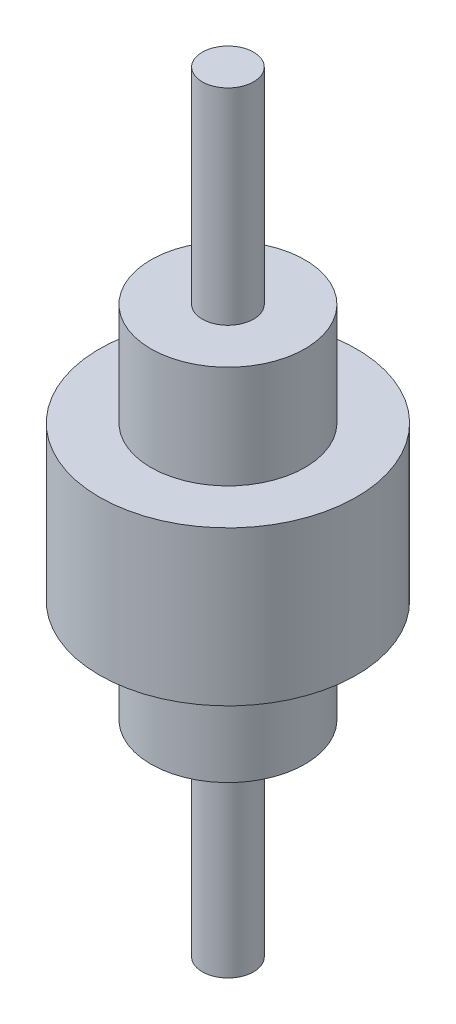
SolidWorks part; units mm, degrees
ref_plane "Front Plane" through (0, 0, 0) normal (0, 0, 1) x (1, 0, 0)
ref_plane "Top Plane" through (0, 0, 0) normal (0, 1, 0) x (1, 0, 0)
ref_plane "Right Plane" through (0, 0, 0) normal (1, 0, 0) x (0, 0, -1)
sketch "Sketch1" plane through (0, 0, 0) normal (0, 0, 1) x (1, 0, 0)
  line L0 (0, 0) -> (0, -203.8323) construction
  line L1 (0, -203.8323) -> (0, 170.1772) construction
  line L2 (10, 48.2971) -> (30, 48.2971)
  line L3 (50, -51.7029) -> (30, -51.7029)
  line L4 (30, 48.2971) -> (30, 8.2971)
  line L5 (30, 8.2971) -> (50, 8.2971)
  line L6 (50, -51.7029) -> (50, 8.2971)
  line L7 (10, 128.2971) -> (0, 128.2971)
  line L8 (10, 48.2971) -> (10, 128.2971)
  line L9 (0, 128.2971) -> (0, -171.7029)
  line L10 (30, -51.7029) -> (30, -91.7029)
  line L11 (30, -91.7029) -> (10, -91.7029)
  line L12 (10, -91.7029) -> (10, -171.7029)
  line L13 (10, -171.7029) -> (0, -171.7029)
  dimension "D3" = 40
  dimension "D5" = 10
  dimension "D2" = 60
  dimension "D4" = 80
  dimension "D6" = 20
  dimension "D7" = 20
revolve "Revolve2" add sketch "Sketch1" angle 360 about L9
